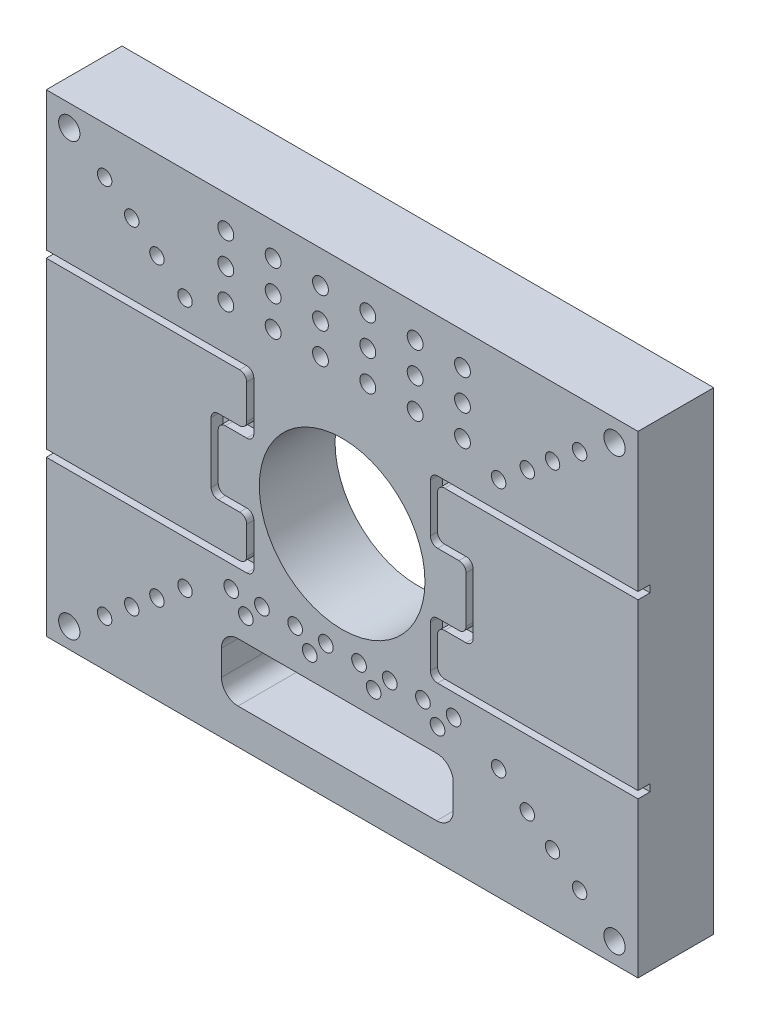
SolidWorks part; units mm, degrees
ref_plane "Alzado" through (0, 0, 0) normal (0, 0, 1) x (1, 0, 0)
ref_plane "Planta" through (0, 0, 0) normal (0, 1, 0) x (1, 0, 0)
ref_plane "Vista lateral" through (0, 0, 0) normal (1, 0, 0) x (0, 0, -1)
sketch "Croquis1" plane through (0, 0, 0) normal (0, 0, 1) x (1, 0, 0)
  line L1 (-125, 100) -> (125, 100)
  line L2 (-125, 100) -> (-125, -100)
  line L3 (-125, -100) -> (125, -100)
  line L4 (125, 100) -> (125, -100)
  line L5 (-125, 100) -> (125, -100) construction
  line L6 (-125, -100) -> (125, 100) construction
  point P0 (0, 0)
  dimension "D1" = 200
  dimension "D2" = 250
extrude "Saliente-Extruir1" add sketch "Croquis1" along normal blind 32
hole_wizard "Taladro de margen para M1.61" positions "Croquis2" profile "Croquis3" hole size "M1.6" standard "Ansi Metric"
sketch "Croquis2" plane through (0, 0, 32) normal (0, 0, 1) x (1, 0, 0)
  line L1 (-125, 100) -> (125, 100) construction
  line L2 (-125, 100) -> (-125, -100) construction
  line L3 (-125, -100) -> (125, -100) construction
  line L4 (125, 100) -> (125, -100) construction
  line L5 (-125, 100) -> (125, -100) construction
  line L6 (-125, -100) -> (125, 100) construction
  line L7 (125, -100) -> (125, 100) construction
  line L8 (125, 100) -> (-125, 100) construction
  point P14 (0, 0)
  point P67 (-66.3791, 53.1033)
  point P85 (66.1169, 52.8935)
  point P105 (-78.2417, 62.5934)
  point P107 (-88.8935, 71.1148)
  point P109 (-100.333, 80.2664)
  point P111 (78.2417, 62.5934)
  point P113 (88.8935, 71.1148)
  point P115 (100.333, 80.2664)
sketch "Croquis3" plane through (0, 0, 32) normal (1, 0, 0) x (0, -1, 0)
  line L0 (0, 0) -> (0, 21.8326)
  line L1 (0, 21.8326) -> (3.05, 20)
  line L2 (3.05, 20) -> (3.05, 0)
  line L5 (3.05, 0) -> (0, 0)
  line L10 (0, 21.8326) -> (-3.05, 20) construction
  line L11 (0, -6.35) -> (0, 107.95) construction
  dimension "Diámetro de taladro" = 6.1
  dimension "Profundidad de taladro" = 20
  dimension "Ángulo de perforador" = 118
hole_wizard "Taladro1" positions "Croquis4" profile "Croquis5" legacy end condition through all
sketch "Croquis4" plane through (0, 0, 32) normal (0, 0, 1) x (1, 0, 0)
  point P0 (0, 0)
sketch "Croquis5" plane through (0, 0, 32) normal (1, 0, 0) x (0, -1, 0)
  line L0 (0, 0) -> (0, 32)
  line L1 (0, 32) -> (35, 32)
  line L2 (35, 32) -> (35, 0)
  line L3 (35, 0) -> (0, 0)
  line L4 (0, 110) -> (0, -10) construction
  dimension "Diámetro" = 70
  dimension "Profundidad" = 32
hole_wizard "Taladro2" positions "Croquis6" profile "Croquis7" legacy
sketch "Croquis6" plane through (0, 0, 32) normal (0, 0, 1) x (1, 0, 0)
  point P0 (-49.1533, 86.2673)
sketch "Croquis7" plane through (-49.1533, 86.2673, 32) normal (1, 0, 0) x (0, -1, 0)
  line L0 (0, 0) -> (0, 27.4)
  line L1 (0, 27.4) -> (3.35, 27.4)
  line L2 (3.35, 27.4) -> (3.35, 0)
  line L3 (3.35, 0) -> (0, 0)
  line L4 (0, 110) -> (0, -10) construction
  dimension "Diámetro" = 6.7
  dimension "Profundidad" = 27.4
pattern_linear "MatrizL1" count 6 spacing 20 along (1, 0, 0) count 3 spacing 13 along (0, -1, 0) of "Taladro2"
sketch "Croquis8" plane through (0, 0, 32) normal (0, 0, 1) x (1, 0, 0)
  line L1 (-43.9969, -60.3224) -> (39.9341, -60.3224)
  line L2 (-50.9969, -67.3224) -> (-50.9969, -77.9929)
  line L3 (-43.9969, -84.9929) -> (39.9341, -84.9929)
  line L4 (46.9341, -67.3224) -> (46.9341, -77.9929)
  line L5 (-50.9969, -60.3224) -> (46.9341, -84.9929) construction
  line L6 (-50.9969, -84.9929) -> (46.9341, -60.3224) construction
  arc A0 (39.9341, -84.9929) -> (46.9341, -77.9929) centre (39.9341, -77.9929) ccw
  arc A1 (39.9341, -60.3224) -> (46.9341, -67.3224) centre (39.9341, -67.3224) cw
  arc A2 (-50.9969, -77.9929) -> (-43.9969, -84.9929) centre (-43.9969, -77.9929) ccw
  arc A3 (-43.9969, -60.3224) -> (-50.9969, -67.3224) centre (-43.9969, -67.3224) ccw
  point P0 (-2.0314, -72.6576)
  dimension "D1" = 7
extrude "Cortar-Extruir1" cut sketch "Croquis8" against normal through all
hole_wizard "Taladro3" positions "Croquis9" profile "Croquis11" legacy
sketch "Croquis9" plane through (0, 0, 32) normal (0, 0, 1) x (1, 0, 0)
  point P12 (-115.2771, 90.8806)
  point P14 (115.0796, 90.8806)
  point P16 (-115.2771, -91.4979)
  point P18 (115.0796, -91.4979)
sketch "Croquis11" plane through (-115.2771, 90.8806, 32) normal (1, 0, 0) x (0, -1, 0)
  line L0 (0, 0) -> (0, 32)
  line L1 (0, 32) -> (4.5, 32)
  line L2 (4.5, 32) -> (4.5, 0)
  line L3 (4.5, 0) -> (0, 0)
  line L4 (0, 110) -> (0, -10) construction
  dimension "Diámetro" = 9
  dimension "Profundidad" = 32
hole_wizard "Taladro de margen para M1.62" positions "Croquis12" profile "Croquis13" hole size "M1.6" standard "Ansi Metric"
sketch "Croquis12" plane through (0, 0, 32) normal (0, 0, 1) x (1, 0, 0)
  point P0 (0, 32.6433)
  point P2 (-32.7937, 0)
  point P4 (30.9886, 0)
  point P6 (0, -30.2364)
sketch "Croquis13" plane through (0, 32.6433, 32) normal (1, 0, 0) x (0, -1, 0)
  line L0 (0, 0) -> (0, 16.3519)
  line L1 (0, 16.3519) -> (2.25, 15)
  line L2 (2.25, 15) -> (2.25, 0)
  line L5 (2.25, 0) -> (0, 0)
  line L10 (0, 16.3519) -> (-2.25, 15) construction
  line L11 (0, -6.35) -> (0, 107.95) construction
  dimension "Diámetro de taladro" = 4.5
  dimension "Profundidad de taladro" = 15
  dimension "Ángulo de perforador" = 118
hole_wizard "Taladro4" positions "Croquis14" profile "Croquis15" legacy
sketch "Croquis14" plane through (0, 0, 32) normal (0, 0, 1) x (1, 0, 0)
  point P0 (-46.8605, -43.6155)
  point P2 (-40.6853, -50.4187)
  point P4 (-33.8822, -43.6155)
sketch "Croquis15" plane through (-46.8605, -43.6155, 32) normal (1, 0, 0) x (0, -1, 0)
  line L0 (0, 0) -> (0, 32)
  line L1 (0, 32) -> (3.1, 32)
  line L2 (3.1, 32) -> (3.1, 0)
  line L3 (3.1, 0) -> (0, 0)
  line L4 (0, 110) -> (0, -10) construction
  dimension "Diámetro" = 6.2
  dimension "Profundidad" = 32
pattern_linear "MatrizL2" count 4 spacing 27 along (1, 0, 0) of "Taladro4"
sketch "Croquis16" plane through (0, 0, 32) normal (0, 0, 1) x (1, 0, 0)
  line L0 (-125, 41.3682) -> (-40.3066, 41.3682)
  line L2 (-125, 100) -> (-125, -100) construction
  line L3 (-37.3066, 38.3682) -> (-37.3066, 17.8926)
  line L4 (-40.3066, 14.8926) -> (-49.3496, 14.8926)
  line L5 (-52.3496, 11.8926) -> (-52.3496, -7.6805)
  line L6 (-49.3496, -10.6805) -> (-40.3066, -10.6805)
  line L7 (-37.3066, -13.6805) -> (-37.3066, -31.4484)
  line L8 (-40.3066, -34.4484) -> (-125, -34.4484)
  line L9 (-125, 38.3682) -> (-43.3066, 38.3682)
  line L10 (-40.3066, 35.3682) -> (-40.3066, 20.8926)
  line L11 (-43.3066, 17.8926) -> (-52.3496, 17.8926)
  line L12 (-55.3496, 14.8926) -> (-55.3496, -10.6805)
  line L13 (-52.3496, -13.6805) -> (-43.3066, -13.6805)
  line L14 (-40.3066, -16.6805) -> (-40.3066, -28.4484)
  line L15 (-43.3066, -31.4484) -> (-125, -31.4484)
  line L16 (-125, 41.3682) -> (-125, 38.3682)
  line L17 (-125, -34.4484) -> (-125, -31.4484)
  line L18 (-40.3066, -13.6805) -> (-40.3066, -31.4484) construction
  line L19 (-40.3066, -31.4484) -> (-125, -31.4484) construction
  line L20 (-55.3496, -13.6805) -> (-40.3066, -13.6805) construction
  line L21 (-52.3496, 14.8926) -> (-52.3496, -10.6805) construction
  line L22 (-52.3496, -10.6805) -> (-37.3066, -10.6805) construction
  line L23 (-55.3496, 17.8926) -> (-55.3496, -13.6805) construction
  line L24 (-37.3066, 14.8926) -> (-52.3496, 14.8926) construction
  line L25 (-40.3066, 17.8926) -> (-55.3496, 17.8926) construction
  line L26 (-40.3066, 38.3682) -> (-40.3066, 17.8926) construction
  line L27 (-125, 38.3682) -> (-40.3066, 38.3682) construction
  line L28 (-37.3066, -10.6805) -> (-37.3066, -34.4484) construction
  line L29 (-37.3066, -34.4484) -> (-125, -34.4484) construction
  line L30 (-37.3066, 41.3682) -> (-37.3066, 14.8926) construction
  line L31 (-125, 41.3682) -> (-37.3066, 41.3682) construction
  arc A0 (-40.3066, -28.4484) -> (-43.3066, -31.4484) centre (-43.3066, -28.4484) cw
  arc A1 (-43.3066, -13.6805) -> (-40.3066, -16.6805) centre (-43.3066, -16.6805) cw
  arc A2 (-52.3496, -7.6805) -> (-49.3496, -10.6805) centre (-49.3496, -7.6805) ccw
  arc A3 (-55.3496, -10.6805) -> (-52.3496, -13.6805) centre (-52.3496, -10.6805) ccw
  arc A4 (-49.3496, 14.8926) -> (-52.3496, 11.8926) centre (-49.3496, 11.8926) ccw
  arc A5 (-52.3496, 17.8926) -> (-55.3496, 14.8926) centre (-52.3496, 14.8926) ccw
  arc A6 (-40.3066, 20.8926) -> (-43.3066, 17.8926) centre (-43.3066, 20.8926) cw
  arc A7 (-43.3066, 38.3682) -> (-40.3066, 35.3682) centre (-43.3066, 35.3682) cw
  arc A8 (-37.3066, -31.4484) -> (-40.3066, -34.4484) centre (-40.3066, -31.4484) cw
  arc A9 (-40.3066, -10.6805) -> (-37.3066, -13.6805) centre (-40.3066, -13.6805) cw
  arc A10 (-37.3066, 17.8926) -> (-40.3066, 14.8926) centre (-40.3066, 17.8926) cw
  arc A11 (-40.3066, 41.3682) -> (-37.3066, 38.3682) centre (-40.3066, 38.3682) cw
  dimension "D2" = 3
  dimension "D1" = 3
extrude "Cortar-Extruir2" cut sketch "Croquis16" against normal blind 5.1
mirror "Simetría1" about plane through (0, 0, 0) normal (1, 0, 0) of "Cortar-Extruir2"
mirror "Simetría2" about plane through (0, 0, 0) normal (0, 1, 0) of "Taladro de margen para M1.61"
